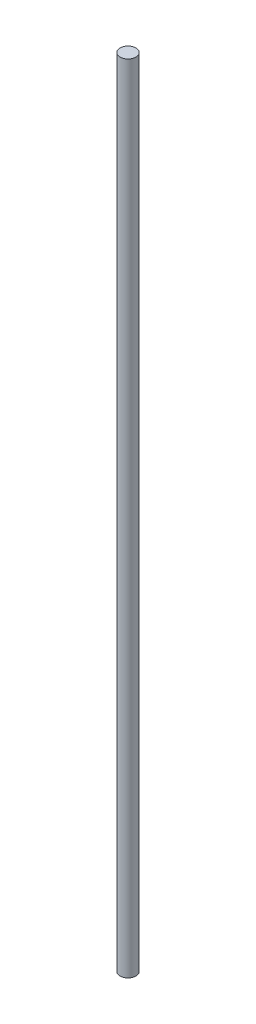
SolidWorks part; units mm, degrees
material "Stainless Steel (ferritic)"
ref_plane "Front Plane" through (0, 0, 0) normal (0, 0, 1) x (1, 0, 0)
ref_plane "Top Plane" through (0, 0, 0) normal (0, 1, 0) x (1, 0, 0)
ref_plane "Right Plane" through (0, 0, 0) normal (1, 0, 0) x (0, 0, -1)
sketch "Sketch1" plane through (0, 0, 0) normal (0, 1, 0) x (1, 0, 0)
  circle A0 centre (0, 0) radius 5
  dimension "D1" = 10
extrude "Boss-Extrude1" add sketch "Sketch1" along normal blind 500
